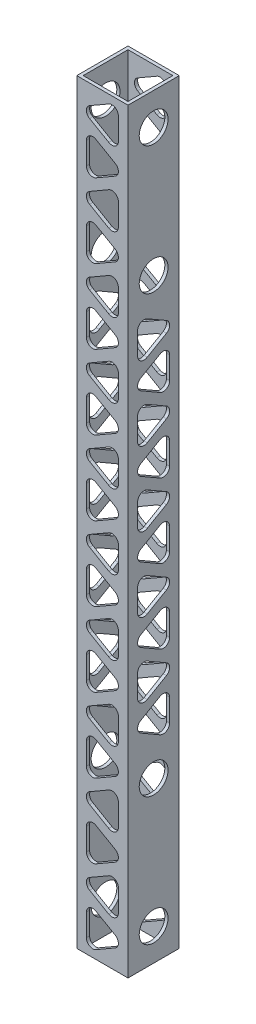
SolidWorks part; units mm, degrees
material "6061 Alloy"
ref_plane "Front Plane" through (0, 0, 0) normal (0, 0, 1) x (1, 0, 0)
ref_plane "Top Plane" through (0, 0, 0) normal (0, 1, 0) x (1, 0, 0)
ref_plane "Right Plane" through (0, 0, 0) normal (1, 0, 0) x (0, 0, -1)
sketch "Sketch1" plane through (0, 0, 0) normal (0, 1, 0) x (1, 0, 0)
  line L0 (-25.4, -25.4) -> (25.4, 25.4) construction
  line L1 (-25.4, 25.4) -> (25.4, 25.4)
  line L2 (-25.4, 25.4) -> (-25.4, -25.4)
  line L3 (-25.4, -25.4) -> (25.4, -25.4)
  line L4 (25.4, 25.4) -> (25.4, -25.4)
  line L5 (22.225, -22.225) -> (-22.225, 22.225) construction
  line L6 (-22.225, 22.225) -> (22.225, 22.225)
  line L7 (-22.225, 22.225) -> (-22.225, -22.225)
  line L8 (-22.225, -22.225) -> (22.225, -22.225)
  line L9 (22.225, 22.225) -> (22.225, -22.225)
  point P7 (0, 0)
  point P10 (0, 0)
  point P14 (0, 0)
  dimension "D1" = 50.8
  dimension "D2" = 3.175
  dimension "D3" = 3.175
  dimension "D4" = 3.175
extrude "Boss-Extrude1" add sketch "Sketch1" along normal blind 749.3
sketch "Sketch2" plane through (-25.4, 0, 0) normal (-1, 0, 0) x (0, 0, 1)
  line L0 (25.4, 374.65) -> (-25.4, 374.65) construction
  line L1 (25.4, 749.3) -> (25.4, 0) construction
  line L2 (-25.4, 749.3) -> (-25.4, 0) construction
  line L3 (0, 31.75) -> (0, 717.55) construction
  line L4 (0, 590.55) -> (0, 158.75) construction
  circle A0 centre (0, 31.75) radius 14.2875
  circle A1 centre (0, 158.75) radius 14.2875
  circle A2 centre (0, 590.55) radius 14.2875
  circle A3 centre (0, 717.55) radius 14.2875
  point P10 (0, 374.65)
  point P13 (0, 374.65)
  dimension "D3" = 28.575
extrude "Cut-Extrude1" cut sketch "Sketch2" against normal through all
sketch "Sketch3" plane through (25.4, 0, 0) normal (1, 0, 0) x (0, 0, -1)
  line L0 (25.4, 749.3) -> (25.4, 0) construction
  line L1 (-12.7, 203.8796) -> (6.35, 192.8811)
  line L2 (15.875, 198.3803) -> (15.875, 220.3774)
  line L3 (6.35, 225.8767) -> (-12.7, 214.8781)
  line L4 (12.7, 251.5399) -> (-6.35, 262.5384)
  line L5 (-15.875, 257.0391) -> (-15.875, 235.0421)
  line L6 (-6.35, 229.5428) -> (12.7, 240.5413)
  line L7 (-25.4, 749.3) -> (-25.4, 0) construction
  line L8 (-12.7, 277.3497) -> (6.35, 266.3512)
  line L9 (15.875, 271.8505) -> (15.875, 293.8475)
  line L10 (6.35, 299.3468) -> (-12.7, 288.3483)
  line L11 (12.7, 325.01) -> (-6.35, 336.0085)
  line L12 (-15.875, 330.5093) -> (-15.875, 308.5122)
  line L13 (-6.35, 303.013) -> (12.7, 314.0115)
  line L14 (-12.7, 350.8199) -> (6.35, 339.8213)
  line L15 (15.875, 345.3206) -> (15.875, 367.3177)
  line L16 (6.35, 372.8169) -> (-12.7, 361.8184)
  line L17 (12.7, 398.4801) -> (-6.35, 409.4787)
  line L18 (-15.875, 403.9794) -> (-15.875, 381.9823)
  line L19 (-6.35, 376.4831) -> (12.7, 387.4816)
  line L32 (-12.7, 424.29) -> (6.35, 413.2915)
  line L33 (15.875, 418.7907) -> (15.875, 440.7878)
  line L34 (6.35, 446.287) -> (-12.7, 435.2885)
  line L35 (12.7, 471.9503) -> (-6.35, 482.9488)
  line L36 (-15.875, 477.4495) -> (-15.875, 455.4525)
  line L37 (-6.35, 449.9532) -> (12.7, 460.9517)
  line L38 (-12.7, 497.7601) -> (6.35, 486.7616)
  line L39 (15.875, 492.2609) -> (15.875, 514.2579)
  line L40 (6.35, 519.7572) -> (-12.7, 508.7587)
  line L41 (12.7, 545.4204) -> (-6.35, 556.4189)
  line L42 (-15.875, 550.9197) -> (-15.875, 528.9226)
  line L43 (-6.35, 523.4233) -> (12.7, 534.4219)
  line L50 (0, 158.75) -> (3.175, 209.3789) construction
  line L51 (0, 590.55) -> (-3.175, 539.9211) construction
  circle A0 centre (3.175, 209.3789) radius 12.7 construction
  circle A1 centre (-3.175, 246.0406) radius 12.7 construction
  arc A2 (-6.35, 262.5384) -> (-15.875, 257.0391) centre (-9.525, 257.0391) ccw
  arc A3 (-15.875, 235.0421) -> (-6.35, 229.5428) centre (-9.525, 235.0421) ccw
  arc A4 (12.7, 251.5399) -> (12.7, 240.5413) centre (9.525, 246.0406) cw
  arc A5 (15.875, 220.3774) -> (6.35, 225.8767) centre (9.525, 220.3774) ccw
  arc A6 (6.35, 192.8811) -> (15.875, 198.3803) centre (9.525, 198.3803) ccw
  arc A7 (-12.7, 203.8796) -> (-12.7, 214.8781) centre (-9.525, 209.3789) cw
  arc A9 (-12.7, 277.3497) -> (-12.7, 288.3483) centre (-9.525, 282.849) cw
  arc A10 (6.35, 266.3512) -> (15.875, 271.8505) centre (9.525, 271.8505) ccw
  arc A11 (15.875, 293.8475) -> (6.35, 299.3468) centre (9.525, 293.8475) ccw
  arc A12 (12.7, 325.01) -> (12.7, 314.0115) centre (9.525, 319.5107) cw
  arc A13 (-6.35, 336.0085) -> (-15.875, 330.5093) centre (-9.525, 330.5093) ccw
  arc A14 (-15.875, 308.5122) -> (-6.35, 303.013) centre (-9.525, 308.5122) ccw
  arc A15 (-12.7, 350.8199) -> (-12.7, 361.8184) centre (-9.525, 356.3191) cw
  arc A16 (6.35, 339.8213) -> (15.875, 345.3206) centre (9.525, 345.3206) ccw
  arc A17 (15.875, 367.3177) -> (6.35, 372.8169) centre (9.525, 367.3177) ccw
  arc A18 (12.7, 398.4801) -> (12.7, 387.4816) centre (9.525, 392.9809) cw
  arc A19 (-6.35, 409.4787) -> (-15.875, 403.9794) centre (-9.525, 403.9794) ccw
  arc A20 (-15.875, 381.9823) -> (-6.35, 376.4831) centre (-9.525, 381.9823) ccw
  arc A34 (-12.7, 424.29) -> (-12.7, 435.2885) centre (-9.525, 429.7893) cw
  arc A35 (6.35, 413.2915) -> (15.875, 418.7907) centre (9.525, 418.7907) ccw
  arc A36 (15.875, 440.7878) -> (6.35, 446.287) centre (9.525, 440.7878) ccw
  arc A37 (12.7, 471.9503) -> (12.7, 460.9517) centre (9.525, 466.451) cw
  arc A38 (-6.35, 482.9488) -> (-15.875, 477.4495) centre (-9.525, 477.4495) ccw
  arc A39 (-15.875, 455.4525) -> (-6.35, 449.9532) centre (-9.525, 455.4525) ccw
  arc A40 (-12.7, 497.7601) -> (-12.7, 508.7587) centre (-9.525, 503.2594) cw
  arc A41 (6.35, 486.7616) -> (15.875, 492.2609) centre (9.525, 492.2609) ccw
  arc A42 (15.875, 514.2579) -> (6.35, 519.7572) centre (9.525, 514.2579) ccw
  arc A43 (12.7, 545.4204) -> (12.7, 534.4219) centre (9.525, 539.9211) cw
  arc A44 (-6.35, 556.4189) -> (-15.875, 550.9197) centre (-9.525, 550.9197) ccw
  arc A45 (-15.875, 528.9226) -> (-6.35, 523.4233) centre (-9.525, 528.9226) ccw
  circle A52 centre (-3.175, 539.9211) radius 12.7 construction
  point P24 (-15.875, 209.3789)
  point P27 (15.875, 246.0406)
  point P30 (0, 0)
  dimension "D1" = 6.35
  dimension "D7" = 9.652
  dimension "D2" = 9.525
  dimension "D3" = 9.525
  dimension "D4" = 9.525
  dimension "D5" = 9.525
  dimension "D6" = 9.525
  dimension "D10" = 36.6617
  dimension "D8" = 5
extrude "Cut-Extrude2" cut sketch "Sketch3" against normal blind 71.12
sketch "Sketch5" plane through (0, 0, -25.4) normal (0, 0, -1) x (-1, 0, 0)
  line L0 (-3.175, 724.3297) -> (3.175, 687.5213) construction
  line L1 (12.7, 729.829) -> (-6.35, 740.8275)
  line L2 (-15.875, 735.3282) -> (-15.875, 713.3312)
  line L3 (-6.35, 707.8319) -> (12.7, 718.8304)
  line L4 (-12.7, 682.022) -> (6.35, 671.0235)
  line L5 (15.875, 676.5228) -> (15.875, 698.5198)
  line L6 (6.35, 704.0191) -> (-12.7, 693.0206)
  line L9 (25.4, 749.3) -> (25.4, 0) construction
  line L10 (12.7, 656.2122) -> (-6.35, 667.2107)
  line L11 (-15.875, 661.7114) -> (-15.875, 639.7144)
  line L12 (-6.35, 634.2151) -> (12.7, 645.2137)
  line L13 (-12.7, 608.4053) -> (6.35, 597.4067)
  line L14 (15.875, 602.906) -> (15.875, 624.9031)
  line L15 (6.35, 630.4023) -> (-12.7, 619.4038)
  line L16 (12.7, 582.5954) -> (-6.35, 593.5939)
  line L17 (-15.875, 588.0947) -> (-15.875, 566.0976)
  line L18 (-6.35, 560.5984) -> (12.7, 571.5969)
  line L19 (-12.7, 534.7885) -> (6.35, 523.79)
  line L20 (15.875, 529.2892) -> (15.875, 551.2863)
  line L21 (6.35, 556.7855) -> (-12.7, 545.787)
  line L22 (12.7, 508.9786) -> (-6.35, 519.9771)
  line L23 (-15.875, 514.4779) -> (-15.875, 492.4808)
  line L24 (-6.35, 486.9816) -> (12.7, 497.9801)
  line L25 (-12.7, 461.1717) -> (6.35, 450.1732)
  line L26 (15.875, 455.6725) -> (15.875, 477.6695)
  line L27 (6.35, 483.1688) -> (-12.7, 472.1702)
  line L28 (12.7, 435.3618) -> (-6.35, 446.3604)
  line L29 (-15.875, 440.8611) -> (-15.875, 418.8641)
  line L30 (-6.35, 413.3648) -> (12.7, 424.3633)
  line L31 (-12.7, 387.5549) -> (6.35, 376.5564)
  line L32 (15.875, 382.0557) -> (15.875, 404.0527)
  line L33 (6.35, 409.552) -> (-12.7, 398.5535)
  line L47 (0, 705.9255) -> (0, 772.5471) construction
  line L48 (-15.875, 713.3312) -> (15.875, 698.5198) construction
  line L49 (9.525, 724.3297) -> (9.525, 698.5198) construction
  line L50 (15.875, 698.5198) -> (25.4, 698.5198) construction
  line L51 (-15.875, 713.3312) -> (-25.4, 713.3312) construction
  line L52 (-25.4, 749.3) -> (-25.4, 0) construction
  line L64 (12.7, 361.7451) -> (-6.35, 372.7436)
  line L65 (-15.875, 367.2443) -> (-15.875, 345.2473)
  line L66 (-6.35, 339.748) -> (12.7, 350.7465)
  line L67 (-12.7, 313.9382) -> (6.35, 302.9396)
  line L68 (15.875, 308.4389) -> (15.875, 330.4359)
  line L69 (6.35, 335.9352) -> (-12.7, 324.9367)
  line L70 (12.7, 288.1283) -> (-6.35, 299.1268)
  line L71 (-15.875, 293.6275) -> (-15.875, 271.6305)
  line L72 (-6.35, 266.1312) -> (12.7, 277.1298)
  line L73 (-12.7, 240.3214) -> (6.35, 229.3229)
  line L74 (15.875, 234.8221) -> (15.875, 256.8192)
  line L75 (6.35, 262.3184) -> (-12.7, 251.3199)
  line L76 (12.7, 214.5115) -> (-6.35, 225.51)
  line L77 (-15.875, 220.0108) -> (-15.875, 198.0137)
  line L78 (-6.35, 192.5145) -> (12.7, 203.513)
  line L79 (-12.7, 166.7046) -> (6.35, 155.7061)
  line L80 (15.875, 161.2053) -> (15.875, 183.2024)
  line L81 (6.35, 188.7016) -> (-12.7, 177.7031)
  line L82 (12.7, 140.8947) -> (-6.35, 151.8933)
  line L83 (-15.875, 146.394) -> (-15.875, 124.3969)
  line L84 (-6.35, 118.8977) -> (12.7, 129.8962)
  line L85 (-12.7, 93.0878) -> (6.35, 82.0893)
  line L86 (15.875, 87.5886) -> (15.875, 109.5856)
  line L87 (6.35, 115.0849) -> (-12.7, 104.0863)
  line L88 (12.7, 67.278) -> (-6.35, 78.2765)
  line L89 (-15.875, 72.7772) -> (-15.875, 50.7802)
  line L90 (-6.35, 45.2809) -> (12.7, 56.2794)
  line L91 (-12.7, 19.471) -> (6.35, 8.4725)
  line L92 (15.875, 13.9718) -> (15.875, 35.9688)
  line L93 (6.35, 41.4681) -> (-12.7, 30.4696)
  line L94 (-3.175, 724.3297) -> (0, 749.3) construction
  line L95 (-25.4, 749.3) -> (25.4, 749.3) construction
  line L96 (3.175, 24.9703) -> (0, 0) construction
  line L97 (-25.4, 0) -> (25.4, 0) construction
  circle A0 centre (-3.175, 724.3297) radius 12.7 construction
  circle A1 centre (3.175, 687.5213) radius 12.7 construction
  arc A2 (15.875, 698.5198) -> (6.35, 704.0191) centre (9.525, 698.5198) ccw
  arc A3 (6.35, 671.0235) -> (15.875, 676.5228) centre (9.525, 676.5228) ccw
  arc A4 (-12.7, 682.022) -> (-12.7, 693.0206) centre (-9.525, 687.5213) cw
  arc A5 (-15.875, 713.3312) -> (-6.35, 707.8319) centre (-9.525, 713.3312) ccw
  arc A6 (-6.35, 740.8275) -> (-15.875, 735.3282) centre (-9.525, 735.3282) ccw
  arc A7 (12.7, 729.829) -> (12.7, 718.8304) centre (9.525, 724.3297) cw
  arc A8 (12.7, 656.2122) -> (12.7, 645.2137) centre (9.525, 650.7129) cw
  arc A9 (-6.35, 667.2107) -> (-15.875, 661.7114) centre (-9.525, 661.7114) ccw
  arc A10 (-15.875, 639.7144) -> (-6.35, 634.2151) centre (-9.525, 639.7144) ccw
  arc A11 (-12.7, 608.4053) -> (-12.7, 619.4038) centre (-9.525, 613.9045) cw
  arc A12 (6.35, 597.4067) -> (15.875, 602.906) centre (9.525, 602.906) ccw
  arc A13 (15.875, 624.9031) -> (6.35, 630.4023) centre (9.525, 624.9031) ccw
  arc A14 (12.7, 582.5954) -> (12.7, 571.5969) centre (9.525, 577.0961) cw
  arc A15 (-6.35, 593.5939) -> (-15.875, 588.0947) centre (-9.525, 588.0947) ccw
  arc A16 (-15.875, 566.0976) -> (-6.35, 560.5984) centre (-9.525, 566.0976) ccw
  arc A17 (-12.7, 534.7885) -> (-12.7, 545.787) centre (-9.525, 540.2878) cw
  arc A18 (6.35, 523.79) -> (15.875, 529.2892) centre (9.525, 529.2892) ccw
  arc A19 (15.875, 551.2863) -> (6.35, 556.7855) centre (9.525, 551.2863) ccw
  arc A20 (12.7, 508.9786) -> (12.7, 497.9801) centre (9.525, 503.4794) cw
  arc A21 (-6.35, 519.9771) -> (-15.875, 514.4779) centre (-9.525, 514.4779) ccw
  arc A22 (-15.875, 492.4808) -> (-6.35, 486.9816) centre (-9.525, 492.4808) ccw
  arc A23 (-12.7, 461.1717) -> (-12.7, 472.1702) centre (-9.525, 466.671) cw
  arc A24 (6.35, 450.1732) -> (15.875, 455.6725) centre (9.525, 455.6725) ccw
  arc A25 (15.875, 477.6695) -> (6.35, 483.1688) centre (9.525, 477.6695) ccw
  arc A26 (12.7, 435.3618) -> (12.7, 424.3633) centre (9.525, 429.8626) cw
  arc A27 (-6.35, 446.3604) -> (-15.875, 440.8611) centre (-9.525, 440.8611) ccw
  arc A28 (-15.875, 418.8641) -> (-6.35, 413.3648) centre (-9.525, 418.8641) ccw
  arc A29 (-12.7, 387.5549) -> (-12.7, 398.5535) centre (-9.525, 393.0542) cw
  arc A30 (6.35, 376.5564) -> (15.875, 382.0557) centre (9.525, 382.0557) ccw
  arc A31 (15.875, 404.0527) -> (6.35, 409.552) centre (9.525, 404.0527) ccw
  arc A56 (12.7, 361.7451) -> (12.7, 350.7465) centre (9.525, 356.2458) cw
  arc A57 (-6.35, 372.7436) -> (-15.875, 367.2443) centre (-9.525, 367.2443) ccw
  arc A58 (-15.875, 345.2473) -> (-6.35, 339.748) centre (-9.525, 345.2473) ccw
  arc A59 (-12.7, 313.9382) -> (-12.7, 324.9367) centre (-9.525, 319.4374) cw
  arc A60 (6.35, 302.9396) -> (15.875, 308.4389) centre (9.525, 308.4389) ccw
  arc A61 (15.875, 330.4359) -> (6.35, 335.9352) centre (9.525, 330.4359) ccw
  arc A62 (12.7, 288.1283) -> (12.7, 277.1298) centre (9.525, 282.629) cw
  arc A63 (-6.35, 299.1268) -> (-15.875, 293.6275) centre (-9.525, 293.6275) ccw
  arc A64 (-15.875, 271.6305) -> (-6.35, 266.1312) centre (-9.525, 271.6305) ccw
  arc A65 (-12.7, 240.3214) -> (-12.7, 251.3199) centre (-9.525, 245.8206) cw
  arc A66 (6.35, 229.3229) -> (15.875, 234.8221) centre (9.525, 234.8221) ccw
  arc A67 (15.875, 256.8192) -> (6.35, 262.3184) centre (9.525, 256.8192) ccw
  arc A68 (12.7, 214.5115) -> (12.7, 203.513) centre (9.525, 209.0122) cw
  arc A69 (-6.35, 225.51) -> (-15.875, 220.0108) centre (-9.525, 220.0108) ccw
  arc A70 (-15.875, 198.0137) -> (-6.35, 192.5145) centre (-9.525, 198.0137) ccw
  arc A71 (-12.7, 166.7046) -> (-12.7, 177.7031) centre (-9.525, 172.2039) cw
  arc A72 (6.35, 155.7061) -> (15.875, 161.2053) centre (9.525, 161.2053) ccw
  arc A73 (15.875, 183.2024) -> (6.35, 188.7016) centre (9.525, 183.2024) ccw
  arc A74 (12.7, 140.8947) -> (12.7, 129.8962) centre (9.525, 135.3955) cw
  arc A75 (-6.35, 151.8933) -> (-15.875, 146.394) centre (-9.525, 146.394) ccw
  arc A76 (-15.875, 124.3969) -> (-6.35, 118.8977) centre (-9.525, 124.3969) ccw
  arc A77 (-12.7, 93.0878) -> (-12.7, 104.0863) centre (-9.525, 98.5871) cw
  arc A78 (6.35, 82.0893) -> (15.875, 87.5886) centre (9.525, 87.5886) ccw
  arc A79 (15.875, 109.5856) -> (6.35, 115.0849) centre (9.525, 109.5856) ccw
  arc A80 (12.7, 67.278) -> (12.7, 56.2794) centre (9.525, 61.7787) cw
  arc A81 (-6.35, 78.2765) -> (-15.875, 72.7772) centre (-9.525, 72.7772) ccw
  arc A82 (-15.875, 50.7802) -> (-6.35, 45.2809) centre (-9.525, 50.7802) ccw
  arc A83 (-12.7, 19.471) -> (-12.7, 30.4696) centre (-9.525, 24.9703) cw
  arc A84 (6.35, 8.4725) -> (15.875, 13.9718) centre (9.525, 13.9718) ccw
  arc A85 (15.875, 35.9688) -> (6.35, 41.4681) centre (9.525, 35.9688) ccw
  circle A86 centre (3.175, 24.9703) radius 12.7 construction
  point P144 (0, 705.9255)
  dimension "D1" = 6.35
  dimension "D2" = 36.8084
  dimension "D3" = 9.652
  dimension "D5" = 9.525
  dimension "D6" = 9.652
  dimension "D8" = 10
extrude "Cut-Extrude3" cut sketch "Sketch5" against normal blind 71.12
equation "\"D1@Boss-Extrude1\"=\"HoleDist\"+2.5"
